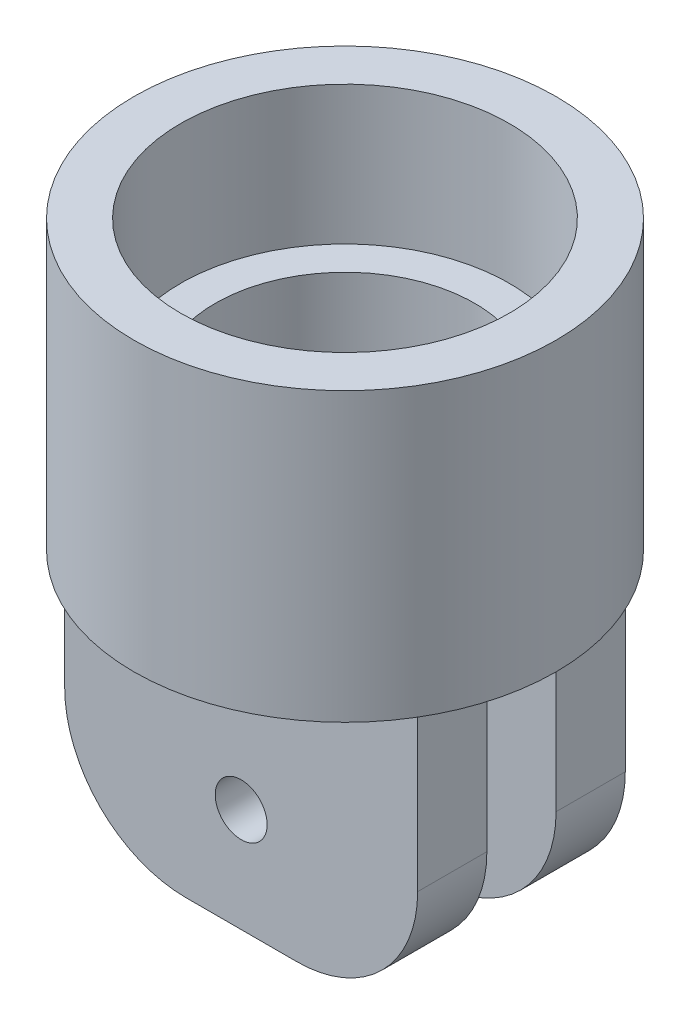
SolidWorks part; units mm, degrees
ref_plane "前视基准面" through (0, 0, 0) normal (0, 0, 1) x (1, 0, 0)
ref_plane "上视基准面" through (0, 0, 0) normal (0, 1, 0) x (1, 0, 0)
ref_plane "右视基准面" through (0, 0, 0) normal (1, 0, 0) x (0, 0, -1)
sketch "草图1" plane through (0, 0, 0) normal (0, 1, 0) x (1, 0, 0)
  circle A0 centre (0, 0) radius 6.1
  dimension "D1" = 12.2
extrude "凸台-拉伸1" add sketch "草图1" along normal blind 8.3
sketch "草图2" plane through (0, 8.3, 0) normal (0, 1, 0) x (1, 0, 0)
  circle A0 centre (0, 0) radius 4.75
  dimension "D1" = 9.5
extrude "切除-拉伸1" cut sketch "草图2" against normal blind 4
sketch "草图3" plane through (0, 4.3, 0) normal (0, 1, 0) x (1, 0, 0)
  circle A0 centre (0, 0) radius 3.75
  circle A1 centre (0, 0) radius 4.75 construction
  dimension "D1" = 1
extrude "切除-拉伸2" cut sketch "草图3" against normal blind 3.5
sketch "草图4" plane through (0, 0.8, 0) normal (0, 1, 0) x (1, 0, 0)
  circle A0 centre (0, 0) radius 1.5
  dimension "D1" = 3
extrude "切除-拉伸3" cut sketch "草图4" against normal blind 4
sketch "草图5" plane through (0, 0, 0) normal (0, 0, 1) x (1, 0, 0)
  line L1 (-6.1, 0) -> (-2.1, 0)
  line L2 (-6.1, 0) -> (-6.1, -4.1)
  line L3 (-4.2, -6) -> (-4, -6)
  line L4 (-2.1, 0) -> (-2.1, -4.1)
  arc A0 (-4, -6) -> (-2.1, -4.1) centre (-4, -4.1) ccw
  arc A1 (-6.1, -4.1) -> (-4.2, -6) centre (-4.2, -4.1) ccw
  dimension "D3" = 1.9
  dimension "D1" = 4
  dimension "D2" = 6
extrude "凸台-拉伸3" add sketch "草图5" along normal mid plane 6
sketch "草图6" plane through (0, 8.3, 0) normal (0, 1, 0) x (1, 0, 0)
  circle A0 centre (0, 0) radius 6.1
  circle A1 centre (0, 0) radius 9.0111
extrude "切除-拉伸4" cut sketch "草图6" against normal blind 32
sketch "草图7" plane through (0, 0, 3) normal (0, 0, 1) x (1, 0, 0)
  line L0 (-4.1, -6.8484) -> (-4.1, 9.077) construction
  line L1 (-4.2, -6) -> (-4, -6) construction
  circle A0 centre (-4.1, -3.8) radius 0.5
  dimension "D2" = 1
  dimension "D1" = 2.2
extrude "切除-拉伸6" cut sketch "草图7" against normal blind 12
sketch "草图8" plane through (-2.1, 0, 0) normal (1, 0, 0) x (0, 0, -1)
  line L0 (-6.1, 0) -> (6.1, 0) construction
  line L1 (-1, 0) -> (1, 0)
  line L2 (-1, 0) -> (-1, -6.9718)
  line L3 (-1, -6.9718) -> (1, -6.9718)
  line L4 (1, 0) -> (1, -6.9718)
  line L5 (3, -4.1) -> (3, 0) construction
  line L6 (-3, -4.1) -> (-3, 0) construction
  dimension "D1" = 2
  dimension "D2" = 2
extrude "切除-拉伸7" cut sketch "草图8" against normal blind 10
sketch "草图9" plane through (0, 0, -3) normal (0, 0, -1) x (-1, 0, 0)
  line L1 (2.1, 0) -> (9.9441, 0)
  line L2 (2.1, 0) -> (2.1, -6.8774)
  line L3 (2.1, -6.8774) -> (9.9441, -6.8774)
  line L4 (9.9441, 0) -> (9.9441, -6.8774)
extrude "切除-拉伸8" cut sketch "草图9" against normal blind 10
sketch "草图10" plane through (0, 0, 0) normal (0, 0, 1) x (1, 0, 0)
  line L0 (-6.1, 0) -> (6.1, 0) construction
  line L1 (-5.1, 0) -> (5.1, 0)
  line L2 (-5.1, 0) -> (-5.1, -4.5)
  line L3 (-1.6, -8) -> (1.6, -8)
  line L4 (5.1, 0) -> (5.1, -4.5)
  line L5 (-6.1, 8.3) -> (-6.1, 0) construction
  line L6 (6.1, 0) -> (6.1, 8.3) construction
  arc A0 (1.6, -8) -> (5.1, -4.5) centre (1.6, -4.5) ccw
  arc A1 (-5.1, -4.5) -> (-1.6, -8) centre (-1.6, -4.5) ccw
  circle A2 centre (0, -5) radius 0.75
  dimension "D4" = 3.5
  dimension "D5" = 1.5
  dimension "D1" = 1
  dimension "D2" = 1
  dimension "D3" = 8
  dimension "D6" = 3
extrude "凸台-拉伸4" add sketch "草图10" along normal mid plane 6
sketch "草图11" plane through (0, -8, 0) normal (0, -1, 0) x (1, 0, 0)
  line L0 (5.1, 3) -> (-5.1, 3) construction
  line L1 (-7.6287, 1) -> (8.0638, 1)
  line L2 (-7.6287, 1) -> (-7.6287, -1)
  line L3 (-7.6287, -1) -> (8.0638, -1)
  line L4 (8.0638, 1) -> (8.0638, -1)
  line L5 (5.1, -3) -> (-5.1, -3) construction
  dimension "D1" = 2
  dimension "D2" = 2
extrude "切除-拉伸9" cut sketch "草图11" against normal up to surface (8 mm away) up to face at (0, 0, 6.1)
